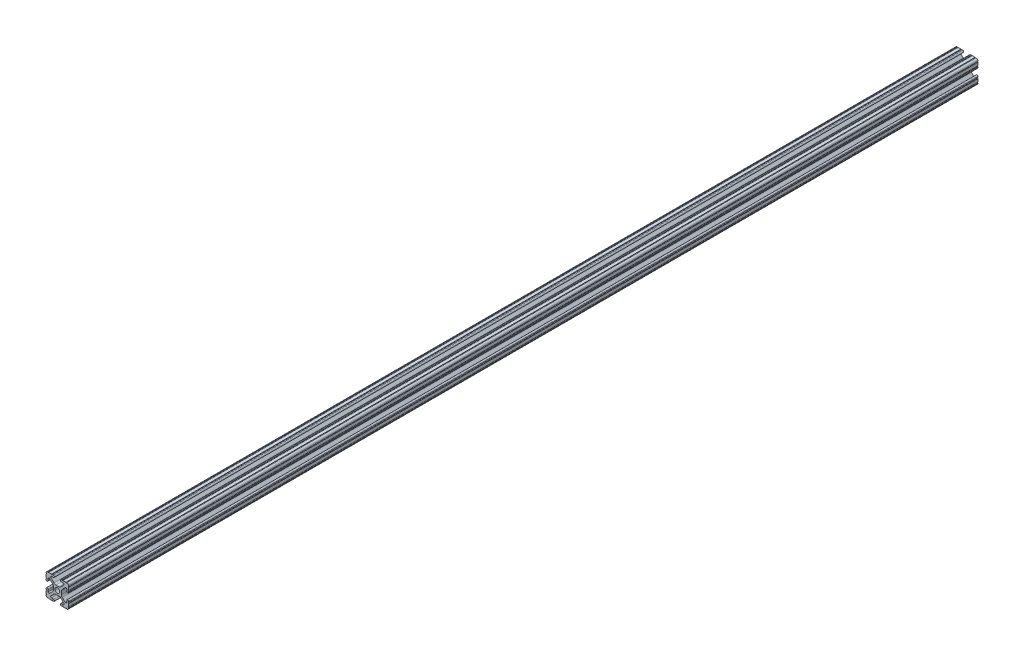
SolidWorks part; units mm, degrees
material "6061-T6 (SS)"
ref_plane "Front Plane" through (0, 0, 0) normal (0, 0, 1) x (1, 0, 0)
ref_plane "Top Plane" through (0, 0, 0) normal (0, 1, 0) x (1, 0, 0)
ref_plane "Right Plane" through (0, 0, 0) normal (1, 0, 0) x (0, 0, -1)
ref_plane "Plane1" through (0, 0, -450.85) normal (0, 0, -1) x (-1, 0, 0)
sketch "Sketch1" plane through (0, 0, -450.85) normal (0, 0, -1) x (-1, 0, 0)
  line L0 (12.7, -9.5504) -> (12.7, -6.3331)
  line L1 (12.7, -5.3171) -> (12.7, -4.3434)
  line L2 (10.4902, -4.3434) -> (10.4902, -6.4748)
  line L3 (8.7558, -7.1932) -> (5.4257, -3.8632)
  line L4 (4.4958, -1.6181) -> (4.4958, 1.6181)
  line L5 (5.4257, 3.8632) -> (8.7558, 7.1932)
  line L6 (10.4902, 6.4748) -> (10.4902, 4.3434)
  line L7 (12.7, 4.3434) -> (12.7, 5.3171)
  line L8 (12.7, 6.3331) -> (12.7, 9.5504)
  line L9 (9.5504, 12.7) -> (6.3331, 12.7)
  line L10 (5.3171, 12.7) -> (4.3434, 12.7)
  line L11 (4.3434, 10.4902) -> (6.4748, 10.4902)
  line L12 (7.1932, 8.7558) -> (3.8632, 5.4257)
  line L13 (1.6181, 4.4958) -> (-1.6181, 4.4958)
  line L14 (-3.8632, 5.4257) -> (-7.1932, 8.7558)
  line L15 (-6.4748, 10.4902) -> (-4.3434, 10.4902)
  line L16 (-4.3434, 12.7) -> (-5.3171, 12.7)
  line L17 (-6.3331, 12.7) -> (-9.5504, 12.7)
  line L18 (-12.7, 9.5504) -> (-12.7, 6.3331)
  line L19 (-12.7, 5.3171) -> (-12.7, 4.3434)
  line L20 (-10.4902, 4.3434) -> (-10.4902, 6.4748)
  line L21 (-8.7558, 7.1932) -> (-5.4257, 3.8632)
  line L22 (-4.4958, 1.6181) -> (-4.4958, -1.6181)
  line L23 (-5.4257, -3.8632) -> (-8.7558, -7.1932)
  line L24 (-10.4902, -6.4748) -> (-10.4902, -4.3434)
  line L25 (-12.7, -4.3434) -> (-12.7, -5.3171)
  line L26 (-12.7, -6.3331) -> (-12.7, -9.5504)
  line L27 (-9.5504, -12.7) -> (-6.3331, -12.7)
  line L28 (-5.3171, -12.7) -> (-4.3434, -12.7)
  line L29 (-4.3434, -10.4902) -> (-6.4748, -10.4902)
  line L30 (-7.1932, -8.7558) -> (-3.8632, -5.4257)
  line L31 (-1.6181, -4.4958) -> (1.6181, -4.4958)
  line L32 (3.8632, -5.4257) -> (7.1932, -8.7558)
  line L33 (6.4748, -10.4902) -> (4.3434, -10.4902)
  line L34 (4.3434, -12.7) -> (5.3171, -12.7)
  line L35 (6.3331, -12.7) -> (9.5504, -12.7)
  arc A0 (12.6998, -10.5664) -> (12.7, -9.5504) centre (12.7, -10.0584) cw
  arc A1 (12.7, -6.3331) -> (12.7, -5.3171) centre (12.7, -5.8251) cw
  arc A2 (12.7, -4.3434) -> (10.4902, -4.3434) centre (11.5951, -4.3434) ccw
  arc A3 (10.4902, -6.4748) -> (8.7558, -7.1932) centre (9.4742, -6.4748) cw
  arc A4 (5.4257, -3.8632) -> (4.4958, -1.6181) centre (7.6708, -1.6181) cw
  arc A5 (4.4958, 1.6181) -> (5.4257, 3.8632) centre (7.6708, 1.6181) cw
  arc A6 (8.7558, 7.1932) -> (10.4902, 6.4748) centre (9.4742, 6.4748) cw
  arc A7 (10.4902, 4.3434) -> (12.7, 4.3434) centre (11.5951, 4.3434) ccw
  arc A8 (12.7, 5.3171) -> (12.7, 6.3331) centre (12.7, 5.8251) cw
  arc A9 (12.7, 9.5504) -> (12.6998, 10.5664) centre (12.7, 10.0584) cw
  arc A10 (12.6998, 10.5664) -> (10.5664, 12.6998) centre (10.5918, 10.5918) ccw
  arc A11 (10.5664, 12.6998) -> (9.5504, 12.7) centre (10.0584, 12.7) cw
  arc A12 (6.3331, 12.7) -> (5.3171, 12.7) centre (5.8251, 12.7) cw
  arc A13 (4.3434, 12.7) -> (4.3434, 10.4902) centre (4.3434, 11.5951) ccw
  arc A14 (6.4748, 10.4902) -> (7.1932, 8.7558) centre (6.4748, 9.4742) cw
  arc A15 (3.8632, 5.4257) -> (1.6181, 4.4958) centre (1.6181, 7.6708) cw
  arc A16 (-1.6181, 4.4958) -> (-3.8632, 5.4257) centre (-1.6181, 7.6708) cw
  arc A17 (-7.1932, 8.7558) -> (-6.4748, 10.4902) centre (-6.4748, 9.4742) cw
  arc A18 (-4.3434, 10.4902) -> (-4.3434, 12.7) centre (-4.3434, 11.5951) ccw
  arc A19 (-5.3171, 12.7) -> (-6.3331, 12.7) centre (-5.8251, 12.7) cw
  arc A20 (-9.5504, 12.7) -> (-10.5664, 12.6998) centre (-10.0584, 12.7) cw
  arc A21 (-10.5664, 12.6998) -> (-12.6998, 10.5664) centre (-10.5918, 10.5918) ccw
  arc A22 (-12.6998, 10.5664) -> (-12.7, 9.5504) centre (-12.7, 10.0584) cw
  arc A23 (-12.7, 6.3331) -> (-12.7, 5.3171) centre (-12.7, 5.8251) cw
  arc A24 (-12.7, 4.3434) -> (-10.4902, 4.3434) centre (-11.5951, 4.3434) ccw
  arc A25 (-10.4902, 6.4748) -> (-8.7558, 7.1932) centre (-9.4742, 6.4748) cw
  arc A26 (-5.4257, 3.8632) -> (-4.4958, 1.6181) centre (-7.6708, 1.6181) cw
  arc A27 (-4.4958, -1.6181) -> (-5.4257, -3.8632) centre (-7.6708, -1.6181) cw
  arc A28 (-8.7558, -7.1932) -> (-10.4902, -6.4748) centre (-9.4742, -6.4748) cw
  arc A29 (-10.4902, -4.3434) -> (-12.7, -4.3434) centre (-11.5951, -4.3434) ccw
  arc A30 (-12.7, -5.3171) -> (-12.7, -6.3331) centre (-12.7, -5.8251) cw
  arc A31 (-12.7, -9.5504) -> (-12.6998, -10.5664) centre (-12.7, -10.0584) cw
  arc A32 (-12.6998, -10.5664) -> (-10.5664, -12.6998) centre (-10.5918, -10.5918) ccw
  arc A33 (-10.5664, -12.6998) -> (-9.5504, -12.7) centre (-10.0584, -12.7) cw
  arc A34 (-6.3331, -12.7) -> (-5.3171, -12.7) centre (-5.8251, -12.7) cw
  arc A35 (-4.3434, -12.7) -> (-4.3434, -10.4902) centre (-4.3434, -11.5951) ccw
  arc A36 (-6.4748, -10.4902) -> (-7.1932, -8.7558) centre (-6.4748, -9.4742) cw
  arc A37 (-3.8632, -5.4257) -> (-1.6181, -4.4958) centre (-1.6181, -7.6708) cw
  arc A38 (1.6181, -4.4958) -> (3.8632, -5.4257) centre (1.6181, -7.6708) cw
  arc A39 (7.1932, -8.7558) -> (6.4748, -10.4902) centre (6.4748, -9.4742) cw
  arc A40 (4.3434, -10.4902) -> (4.3434, -12.7) centre (4.3434, -11.5951) ccw
  arc A41 (5.3171, -12.7) -> (6.3331, -12.7) centre (5.8251, -12.7) cw
  arc A42 (9.5504, -12.7) -> (10.5664, -12.6998) centre (10.0584, -12.7) cw
  arc A43 (10.5664, -12.6998) -> (12.6998, -10.5664) centre (10.5918, -10.5918) ccw
  circle A44 centre (0, 0) radius 2.6035
extrude "Boss-Extrude1" add sketch "Sketch1" against normal blind 1016
